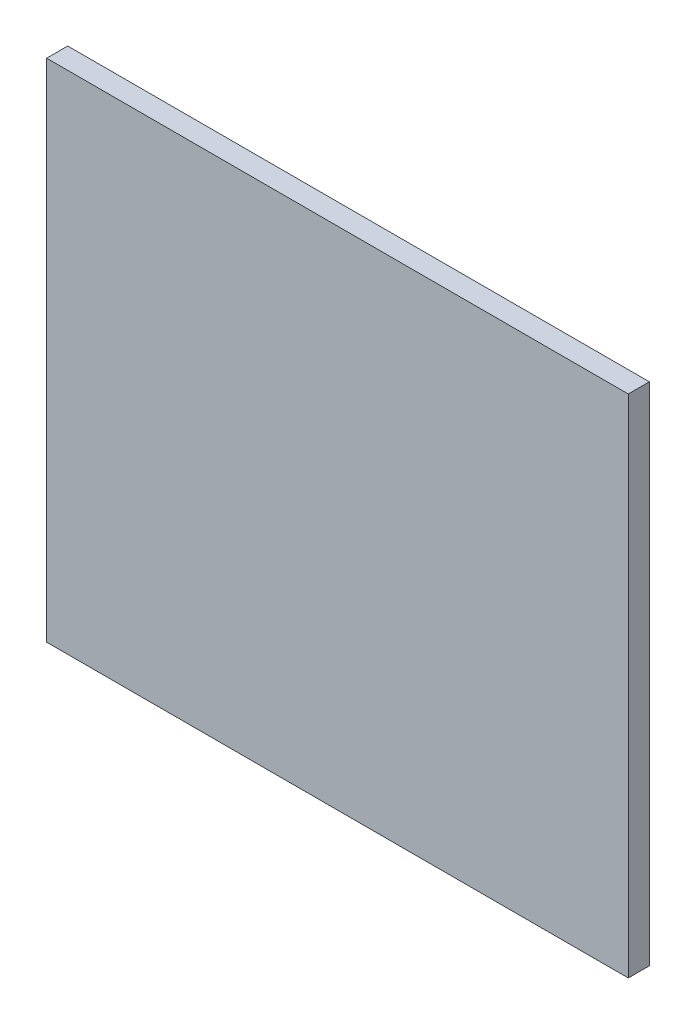
SolidWorks part; units mm, degrees
ref_plane "Front Plane" through (0, 0, 0) normal (0, 0, 1) x (1, 0, 0)
ref_plane "Top Plane" through (0, 0, 0) normal (0, 1, 0) x (1, 0, 0)
ref_plane "Right Plane" through (0, 0, 0) normal (1, 0, 0) x (0, 0, -1)
sketch "Sketch1" plane through (0, 0, 0) normal (0, 0, 1) x (1, 0, 0)
  line L1 (-43.815, 38.1) -> (43.815, 38.1)
  line L2 (-43.815, 38.1) -> (-43.815, -38.1)
  line L3 (-43.815, -38.1) -> (43.815, -38.1)
  line L4 (43.815, 38.1) -> (43.815, -38.1)
  dimension "D1" = 87.63
  dimension "D2" = 76.2
  dimension "D3" = 38.1
  dimension "D4" = 43.815
extrude "Boss-Extrude1" add sketch "Sketch1" along normal blind 3.175
equation "\"D3@Sketch1\"=\"D2@Sketch1\"/2"
equation "\"D4@Sketch1\"=\"D1@Sketch1\"/2"
